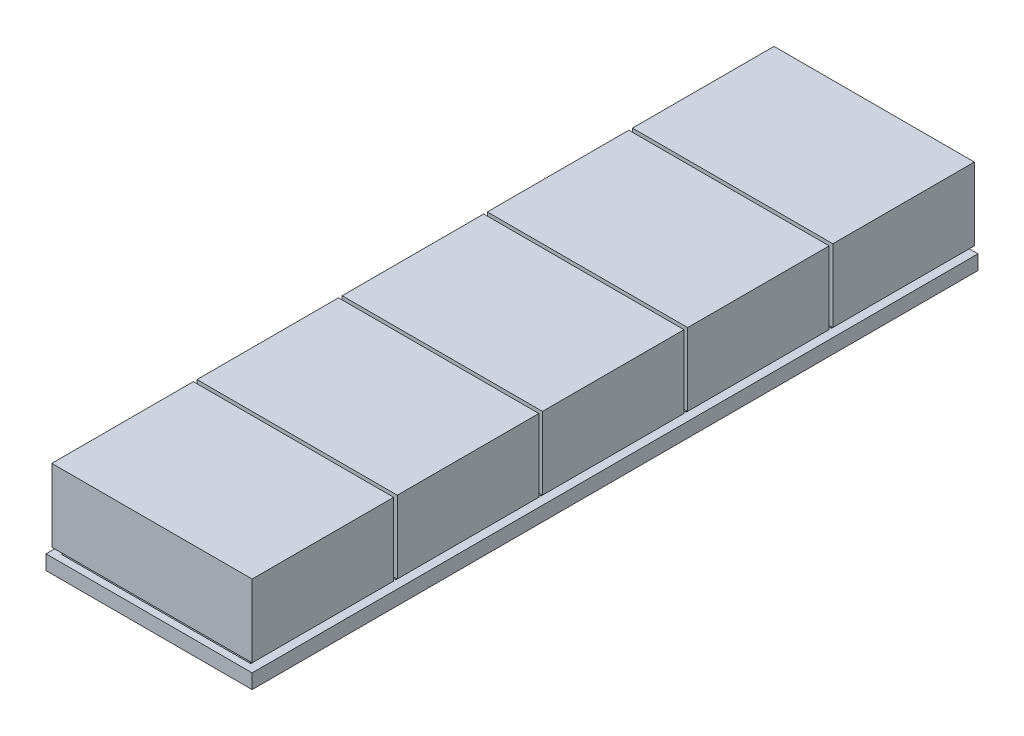
SolidWorks part; units mm, degrees
ref_plane "Front Plane" through (0, 0, 0) normal (0, 0, 1) x (1, 0, 0)
ref_plane "Top Plane" through (0, 0, 0) normal (0, 1, 0) x (1, 0, 0)
ref_plane "Right Plane" through (0, 0, 0) normal (1, 0, 0) x (0, 0, -1)
sketch "Sketch1" plane through (0, 0, 0) normal (0, 1, 0) x (1, 0, 0)
  line L1 (-35.5, -125) -> (35.5, -125)
  line L2 (-35.5, -125) -> (-35.5, 125)
  line L3 (-35.5, 125) -> (35.5, 125)
  line L4 (35.5, -125) -> (35.5, 125)
  line L5 (-35.5, -125) -> (35.5, 125) construction
  line L6 (-35.5, 125) -> (35.5, -125) construction
  point P0 (0, 0)
  dimension "D1" = 71
  dimension "D2" = 250
extrude "Boss-Extrude1" add sketch "Sketch1" along normal blind 5
sketch "Sketch2" plane through (0, 5, 0) normal (0, 1, 0) x (1, 0, 0)
  line L0 (0, 0) -> (0, -125) construction
  line L1 (-35.5, -125) -> (35.5, -125) construction
  line L3 (-32.5, -77.5) -> (32.5, -77.5)
  line L4 (-32.5, -77.5) -> (-32.5, -122.5)
  line L5 (-32.5, -122.5) -> (32.5, -122.5)
  line L6 (32.5, -77.5) -> (32.5, -122.5)
  line L7 (-32.5, -77.5) -> (32.5, -122.5) construction
  line L8 (-32.5, -122.5) -> (32.5, -77.5) construction
  point P5 (0, -100)
  dimension "D1" = 65
  dimension "D2" = 45
  dimension "D3" = 2.5
extrude "Boss-Extrude3" add sketch "Sketch2" along normal blind 2
pattern_linear "LPattern1" count 5 spacing 50 along (0, 0, -1) of "Boss-Extrude3"
sketch "Sketch3" plane through (0, 7, 0) normal (0, 1, 0) x (1, 0, 0)
  line L0 (0, 0) -> (0, -122.5) construction
  line L1 (-32.5, -122.5) -> (32.5, -122.5) construction
  line L2 (-35.5, 125) -> (-35.5, -125) construction
  line L3 (-34.5, -75.2576) -> (34.5, -75.2576)
  line L4 (-34.5, -75.2576) -> (-34.5, -124.0124)
  line L5 (-34.5, -124.0124) -> (34.5, -124.0124)
  line L6 (34.5, -75.2576) -> (34.5, -124.0124)
  line L7 (-34.5, -75.2576) -> (34.5, -124.0124) construction
  line L8 (-34.5, -124.0124) -> (34.5, -75.2576) construction
  point P5 (0, -99.635)
  dimension "D1" = 1
extrude "Boss-Extrude8" add sketch "Sketch3" along normal blind 25
pattern_linear "LPattern5" count 5 spacing 50 along (0, 0, -1) of "Boss-Extrude8"
